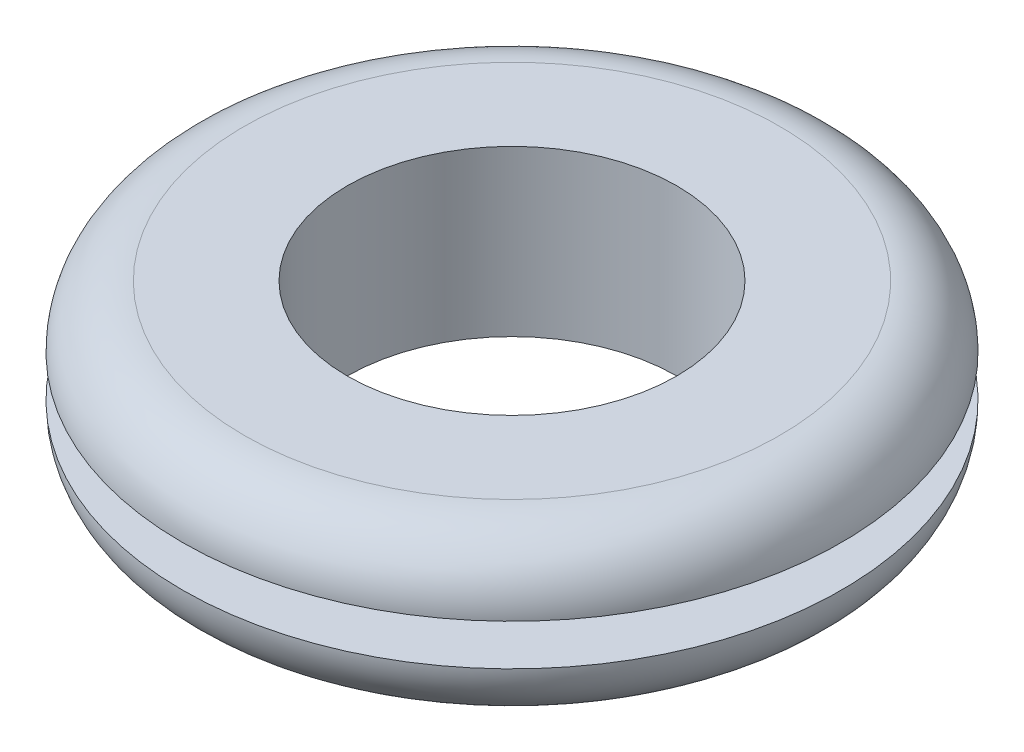
SolidWorks part; units mm, degrees
ref_plane "Front" through (0, 0, 0) normal (0, 0, 1) x (1, 0, 0)
ref_plane "Top" through (0, 0, 0) normal (0, 1, 0) x (1, 0, 0)
ref_plane "Right" through (0, 0, 0) normal (1, 0, 0) x (0, 0, -1)
sketch "Sketch1" plane through (0, 0, 0) normal (0, 0, 1) x (1, 0, 0)
  line L0 (-6.35, 0) -> (6.35, 0) construction
  line L1 (-9.525, 0) -> (9.525, 0) construction
  line L2 (0, 3.175) -> (0, -3.175) construction
  line L3 (12.7, 3.175) -> (-12.7, 3.175) construction
  line L4 (9.525, 0.7937) -> (9.525, -0.7937) construction
  dimension "ID" = 12.7
  dimension "for hole dia" = 19.05
  dimension "oall ht" = 6.35
  dimension "flange dia" = 25.4
  dimension "material thick" = 1.5875
sketch "Sketch2" plane through (0, 0, 0) normal (0, 0, 1) x (1, 0, 0)
  line L0 (9.525, 0.7937) -> (12.7, 0.7938)
  line L1 (12.7, 3.175) -> (12.7, -3.175) construction
  line L2 (12.7, 3.175) -> (-12.7, 3.175) construction
  line L3 (6.35, 3.175) -> (10.3187, 3.175)
  line L4 (9.525, 0.7937) -> (9.525, -0.7937)
  line L5 (6.35, 3.175) -> (6.35, -3.175)
  line L6 (6.35, -3.175) -> (10.3187, -3.175)
  line L7 (12.7, -0.7937) -> (9.525, -0.7937)
  arc A0 (10.3187, 3.175) -> (12.7, 0.7938) centre (10.3187, 0.7937) cw
  arc A1 (10.3187, -3.175) -> (12.7, -0.7937) centre (10.3187, -0.7937) ccw
revolve "Revolve1" add sketch "Sketch2" angle 360 about L2
